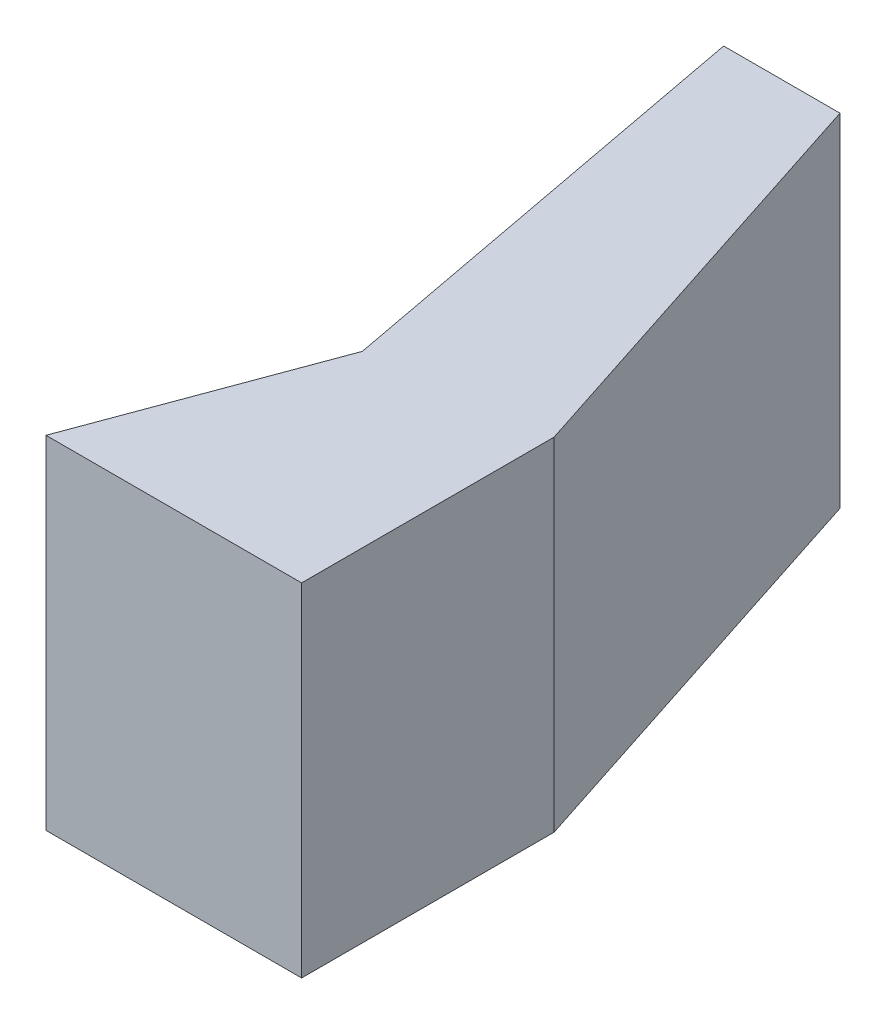
SolidWorks part; units mm, degrees
ref_plane "Front Plane" through (0, 0, 0) normal (0, 0, 1) x (1, 0, 0)
ref_plane "Top Plane" through (0, 0, 0) normal (0, 1, 0) x (1, 0, 0)
ref_plane "Right Plane" through (0, 0, 0) normal (1, 0, 0) x (0, 0, -1)
sketch "Sketch1" plane through (0, 0, 0) normal (0, 1, 0) x (1, 0, 0)
  line L0 (23.0024, -47.0579) -> (-38.9976, -47.0579)
  line L1 (-38.9976, -47.0579) -> (-18.2647, 8.9305)
  line L2 (-18.2647, 8.9305) -> (-38.5888, 116.9062)
  line L3 (-38.5888, 116.9062) -> (-10.3715, 116.9062)
  line L4 (-10.3715, 116.9062) -> (23.0024, 14.1921)
  line L5 (23.0024, 14.1921) -> (23.0024, -47.0579)
  line L6 (-36.1243, -45.0579) -> (21.0024, -45.0579)
  line L7 (21.0024, -45.0579) -> (21.0024, 13.8754)
  line L8 (21.0024, 13.8754) -> (-11.8245, 114.9062)
  line L9 (-11.8245, 114.9062) -> (-36.1773, 114.9062)
  line L10 (-36.1773, 114.9062) -> (-16.1967, 8.7558)
  line L11 (-16.1967, 8.7558) -> (-36.1243, -45.0579)
  dimension "D1" = 62
  dimension "D2" = 69.68
  dimension "D3" = 162
  dimension "D4" = 210.98
  dimension "D5" = 61.25
  dimension "D6" = 108
  dimension "D7" = 2
  dimension "D8" = 2
  dimension "D9" = 2
  dimension "D10" = 2
  dimension "D11" = 2
  dimension "D12" = 2
extrude "Boss-Extrude1" add sketch "Sketch1" along normal blind 81
sketch "Sketch2" plane through (0, 81, 0) normal (0, 1, 0) x (1, 0, 0)
  line L0 (-38.9976, -47.0579) -> (23.0024, -47.0579)
  line L1 (23.0024, -47.0579) -> (23.0024, 14.1921)
  line L2 (23.0024, 14.1921) -> (-10.3715, 116.9062)
  line L3 (-10.3715, 116.9062) -> (-38.5888, 116.9062)
  line L4 (-38.5888, 116.9062) -> (-18.2647, 8.9305)
  line L5 (-18.2647, 8.9305) -> (-38.9976, -47.0579)
extrude "Boss-Extrude2" add sketch "Sketch2" along normal blind 2
equation "\"thick\"= 2"
equation "\"D1@Boss-Extrude1\"=85-\"thick\"*2"
equation "\"D7@Sketch1\"=\"thick\""
equation "\"D8@Sketch1\"=\"thick\""
equation "\"D9@Sketch1\"=\"thick\""
equation "\"D10@Sketch1\"=\"thick\""
equation "\"D11@Sketch1\"=\"thick\""
equation "\"D1@Boss-Extrude2\"=\"thick\""
